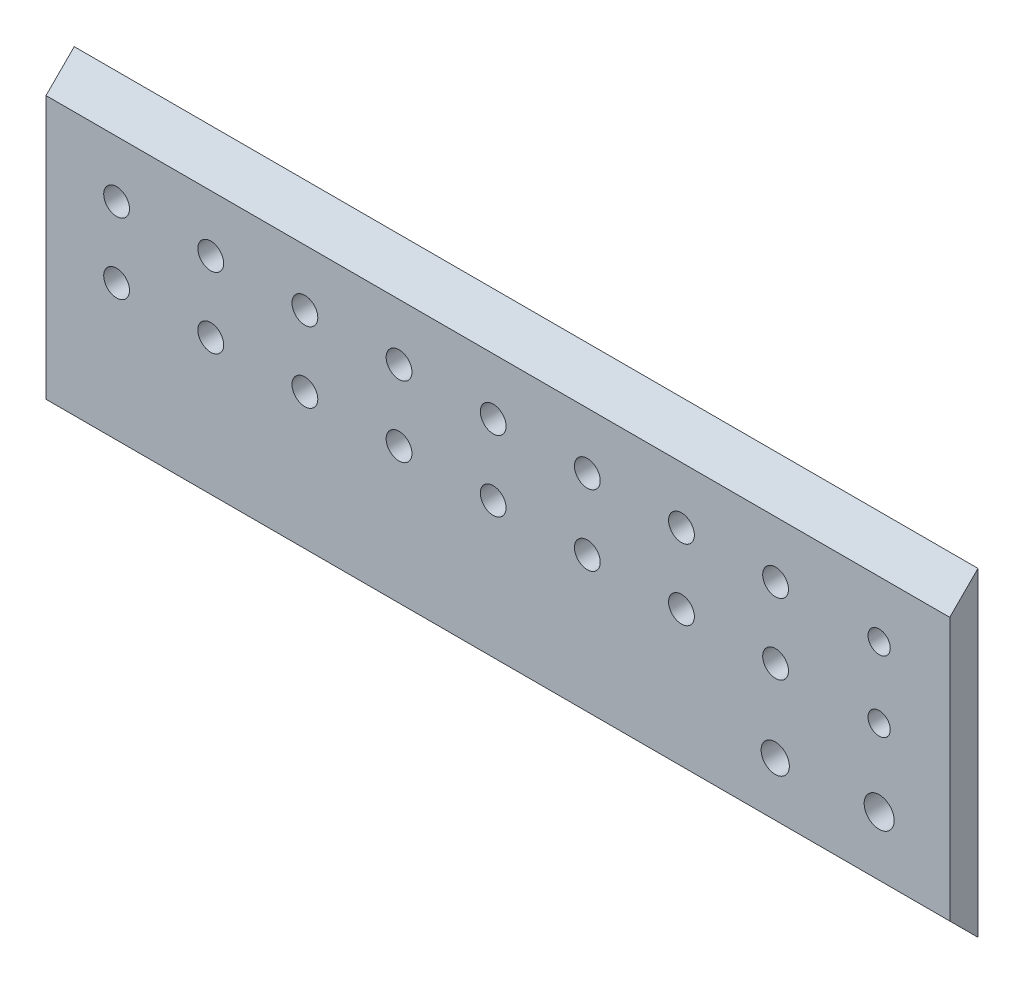
SolidWorks part; units mm, degrees
ref_plane "Front Plane" through (0, 0, 0) normal (0, 0, 1) x (1, 0, 0)
ref_plane "Top Plane" through (0, 0, 0) normal (0, 1, 0) x (1, 0, 0)
ref_plane "Right Plane" through (0, 0, 0) normal (1, 0, 0) x (0, 0, -1)
sketch "Sketch2" plane through (0, 0, 0) normal (0, 0, 1) x (1, 0, 0)
  line L1 (0, 0) -> (203.2, 0)
  line L2 (0, 0) -> (0, 71.842)
  line L3 (0, 71.842) -> (203.2, 71.842)
  line L4 (203.2, 0) -> (203.2, 71.842)
  dimension "D1" = 203.2
  dimension "D2" = 71.842
extrude "Boss-Extrude1" add sketch "Sketch2" along normal blind 6.35
sketch "Sketch3" plane through (0, 0, 0) normal (-1, 0, 0) x (0, 0, 1)
  line L0 (0, 0) -> (6.35, 0)
  line L2 (6.35, 0) -> (6.35, 6.35)
  line L3 (6.35, 71.842) -> (6.35, 0) construction
  line L4 (6.35, 6.35) -> (0, 0)
  dimension "D1" = 6.35
extrude "Cut-Extrude1" cut sketch "Sketch3" against normal blind 203.2
sketch "Sketch5" plane through (0, 0, 0) normal (-1, 0, 0) x (0, 0, 1)
  line L0 (6.35, 71.842) -> (6.35, 65.492)
  line L1 (6.35, 71.842) -> (6.35, 6.35) construction
  line L2 (6.35, 65.492) -> (0, 71.842)
  line L3 (0, 71.842) -> (6.35, 71.842)
  dimension "D1" = 6.35
extrude "Cut-Extrude3" cut sketch "Sketch5" against normal blind 203.2
sketch "Sketch7" plane through (0, 0, 6.35) normal (0, 0, 1) x (1, 0, 0)
  line L0 (0, 65.492) -> (0, 6.35) construction
  line L1 (203.2, 65.492) -> (0, 65.492) construction
  circle A0 centre (15.875, 52.792) radius 2.9
  dimension "D1" = 5.8
  dimension "D2" = 15.875
  dimension "D3" = 12.7
extrude "Cut-Extrude4" cut sketch "Sketch7" against normal blind 6.35
pattern_linear "LPattern1" count 8 spacing 21.1667 along (1, 0, 0) of "Cut-Extrude4"
pattern_linear "LPattern2" count 2 spacing 15.875 along (0, -1, 0) of "LPattern1", "Cut-Extrude4"
sketch "Sketch8" plane through (0, 0, 6.35) normal (0, 0, 1) x (1, 0, 0)
  line L0 (203.2, 65.492) -> (0, 65.492) construction
  line L1 (203.2, 6.35) -> (203.2, 65.492) construction
  circle A0 centre (187.325, 52.792) radius 2.5
  dimension "D1" = 5
  dimension "D2" = 12.7
  dimension "D3" = 15.875
extrude "Cut-Extrude5" cut sketch "Sketch8" against normal blind 6.35
pattern_linear "LPattern3" count 2 spacing 15.875 along (0, -1, 0) of "Cut-Extrude5"
sketch "Sketch9" plane through (0, 0, 6.35) normal (0, 0, 1) x (1, 0, 0)
  line L0 (203.2, 6.35) -> (203.2, 65.492) construction
  circle A0 centre (187.325, 19.6511) radius 3.375
  dimension "D1" = 6.75
  dimension "D2" = 15.875
extrude "Cut-Extrude6" cut sketch "Sketch9" against normal blind 6.35
sketch "Sketch12" plane through (0, 0, 6.35) normal (0, 0, 1) x (1, 0, 0)
  circle A0 centre (163.957, 18.4642) radius 3.175
  circle A2 centre (187.325, 19.6511) radius 3.375 construction
  circle A3 centre (187.325, 52.792) radius 2.5 construction
  circle A4 centre (164.0417, 52.792) radius 2.9 construction
  dimension "D1" = 6.35
  dimension "D2" = 23.368
  dimension "D3" = 23.2833
extrude "Cut-Extrude7" cut sketch "Sketch12" against normal blind 6.35
